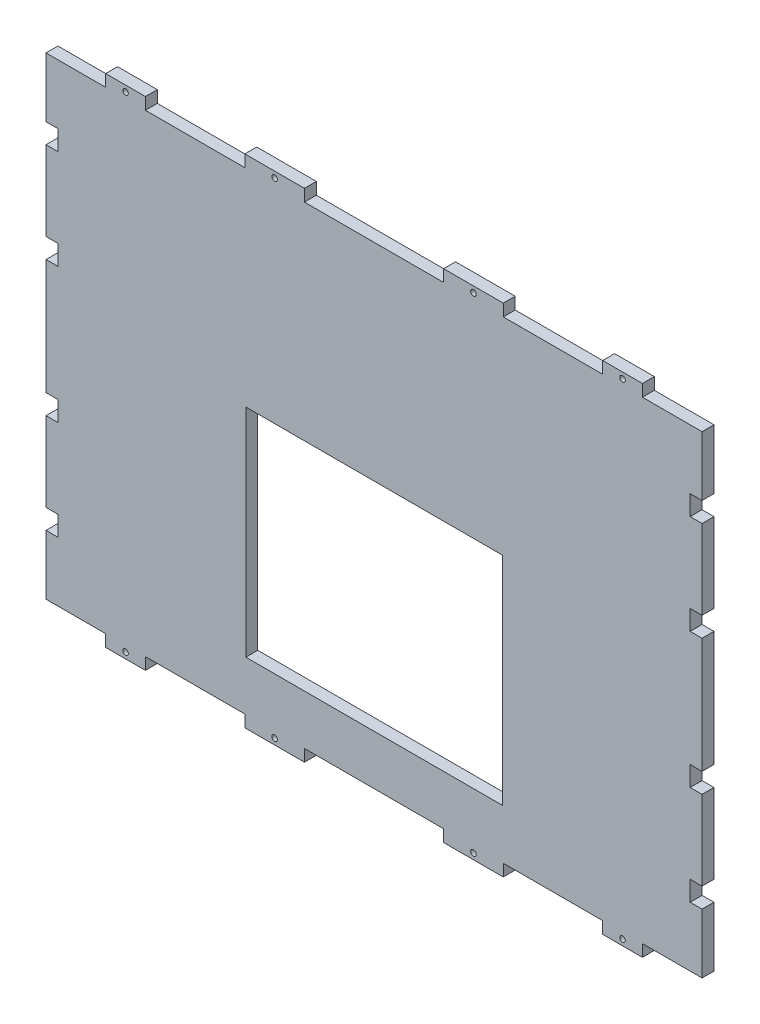
SolidWorks part; units mm, degrees
ref_plane "Plan de face" through (0, 0, 0) normal (0, 0, 1) x (1, 0, 0)
ref_plane "Plan de dessus" through (0, 0, 0) normal (0, 1, 0) x (1, 0, 0)
ref_plane "Plan de droite" through (0, 0, 0) normal (1, 0, 0) x (0, 0, -1)
sketch "Esquisse1" plane through (0, 0, 0) normal (0, 0, 1) x (1, 0, 0)
  line L0 (97.3951, 0) -> (-118.5049, 0) construction
  line L1 (-165, 119) -> (165, 119)
  line L2 (-165, 119) -> (-165, -119)
  line L3 (-165, -119) -> (165, -119)
  line L4 (165, 119) -> (165, -119)
  line L5 (0, 79.3588) -> (0, -79.3588) construction
  dimension "D1" = 238
  dimension "D2" = 330
  dimension "D3" = 165
  dimension "D4" = 119
extrude "Boss.-Extru.1" add sketch "Esquisse1" along normal blind 6
sketch "Esquisse2" plane through (0, 0, 6) normal (0, 0, 1) x (1, 0, 0)
  line L0 (-165, -119) -> (165, -119) construction
  line L1 (-64.5, 15) -> (64.5, 15)
  line L2 (-64.5, 15) -> (-64.5, -94)
  line L3 (-64.5, -94) -> (64.5, -94)
  line L4 (64.5, 15) -> (64.5, -94)
  line L5 (-165, 119) -> (-165, -119) construction
  dimension "D1" = 109
  dimension "D2" = 129
  dimension "D3" = 25
  dimension "D4" = 100.5
extrude "Enlèv. mat.-Extru.1" cut sketch "Esquisse2" against normal blind 6
sketch "Esquisse3" plane through (0, 0, 6) normal (0, 0, 1) x (1, 0, 0)
  line L0 (165, 119) -> (-165, 119) construction
  line L2 (-135, 119) -> (-135, 125)
  line L3 (-135, 125) -> (-115, 125)
  line L4 (-115, 119) -> (-115, 125)
  line L6 (-65, 119) -> (-35, 119)
  line L7 (-65, 119) -> (-65, 125)
  line L8 (-65, 125) -> (-35, 125)
  line L9 (-35, 119) -> (-35, 125)
  line L10 (-165, 119) -> (-165, -119) construction
  line L11 (0, 242.8959) -> (0, -237.5968) construction
  line L12 (383.215, 0) -> (-270.4786, 0) construction
  line L13 (35, 119) -> (35, 125)
  line L14 (65, 125) -> (35, 125)
  line L15 (65, 119) -> (65, 125)
  line L16 (65, 119) -> (35, 119)
  line L17 (115, 119) -> (115, 125)
  line L18 (135, 125) -> (115, 125)
  line L19 (135, 119) -> (135, 125)
  line L20 (135, 119) -> (115, 119)
  line L21 (-135, 119) -> (-115, 119)
  line L22 (-135, 119) -> (-135, 125)
  line L23 (-135, 125) -> (-115, 125)
  line L24 (-115, 119) -> (-115, 125)
  line L25 (-65, 119) -> (-35, 119)
  line L26 (-65, 119) -> (-65, 125)
  line L27 (-65, 125) -> (-35, 125)
  line L28 (-35, 119) -> (-35, 125)
  line L29 (35, 119) -> (35, 125)
  line L30 (65, 125) -> (35, 125)
  line L31 (65, 119) -> (65, 125)
  line L32 (65, 119) -> (35, 119)
  line L33 (115, 119) -> (115, 125)
  line L34 (135, 125) -> (115, 125)
  line L35 (135, 119) -> (135, 125)
  line L36 (135, 119) -> (115, 119)
  line L37 (135, -119) -> (115, -119)
  line L38 (135, -119) -> (135, -125)
  line L39 (135, -125) -> (115, -125)
  line L40 (115, -119) -> (115, -125)
  line L41 (65, -119) -> (35, -119)
  line L42 (65, -119) -> (65, -125)
  line L43 (65, -125) -> (35, -125)
  line L44 (35, -119) -> (35, -125)
  line L45 (-35, -119) -> (-35, -125)
  line L46 (-65, -125) -> (-35, -125)
  line L47 (-65, -119) -> (-65, -125)
  line L48 (-65, -119) -> (-35, -119)
  line L49 (-115, -119) -> (-115, -125)
  line L50 (-135, -125) -> (-115, -125)
  line L51 (-135, -119) -> (-135, -125)
  line L52 (-135, -119) -> (-115, -119)
  line L53 (135, -119) -> (115, -119)
  line L54 (135, -119) -> (135, -125)
  line L55 (135, -125) -> (115, -125)
  line L56 (115, -119) -> (115, -125)
  line L57 (65, -119) -> (35, -119)
  line L58 (65, -119) -> (65, -125)
  line L59 (65, -125) -> (35, -125)
  line L60 (35, -119) -> (35, -125)
  line L61 (-35, -119) -> (-35, -125)
  line L62 (-65, -125) -> (-35, -125)
  line L63 (-65, -119) -> (-65, -125)
  line L64 (-65, -119) -> (-35, -119)
  line L65 (-115, -119) -> (-115, -125)
  line L66 (-135, -125) -> (-115, -125)
  line L67 (-135, -119) -> (-135, -125)
  line L68 (-135, -119) -> (-115, -119)
  line M10 (-165, -119) -> (165, -119)
  line M12 (165, 119) -> (-165, 119)
  dimension "D1" = 20
  dimension "D2" = 6
  dimension "D3" = 6
  dimension "D4" = 30
  dimension "D5" = 50
  dimension "D6" = 30
extrude "Boss.-Extru.4" add sketch "Esquisse3" against normal blind 6 contours L4 L3 L2 M12 | L9 L8 L7 M12 | L15 L14 L13 M12 | L19 L18 L17 M12 | L40 L39 L38 M10 | L44 L43 L42 M10 | L47 L46 L45 M10 | L51 L50 L49 M10
sketch "Esquisse4" plane through (0, 0, 6) normal (0, 0, 1) x (1, 0, 0)
  line L0 (-165, 119) -> (-165, -119) construction
  line L1 (-165, 89) -> (-159, 89)
  line L2 (-165, 89) -> (-165, 79)
  line L3 (-165, 79) -> (-159, 79)
  line L4 (-159, 89) -> (-159, 79)
  line L5 (-135, 119) -> (-165, 119) construction
  line L6 (-165, 39) -> (-159, 39)
  line L7 (-165, 39) -> (-165, 29)
  line L8 (-165, 29) -> (-159, 29)
  line L9 (-159, 39) -> (-159, 29)
  line L12 (258.3547, 0) -> (-305.8943, 0) construction
  line L13 (0, -179.773) -> (0, 204.7522) construction
  line L14 (-159, -89) -> (-159, -79)
  line L15 (-165, -89) -> (-159, -89)
  line L16 (-159, -39) -> (-159, -29)
  line L17 (-165, -29) -> (-159, -29)
  line L18 (-165, -39) -> (-165, -29)
  line L19 (-165, -39) -> (-159, -39)
  line L20 (-165, -79) -> (-159, -79)
  line L21 (-165, -89) -> (-165, -79)
  line L22 (165, -89) -> (165, -79)
  line L23 (165, -79) -> (159, -79)
  line L24 (165, -39) -> (159, -39)
  line L25 (165, -39) -> (165, -29)
  line L26 (165, -29) -> (159, -29)
  line L27 (159, -39) -> (159, -29)
  line L28 (165, -89) -> (159, -89)
  line L29 (159, -89) -> (159, -79)
  line L30 (159, 39) -> (159, 29)
  line L31 (165, 29) -> (159, 29)
  line L32 (165, 39) -> (165, 29)
  line L33 (165, 39) -> (159, 39)
  line L34 (159, 89) -> (159, 79)
  line L35 (165, 79) -> (159, 79)
  line L36 (165, 89) -> (165, 79)
  line L37 (165, 89) -> (159, 89)
  dimension "D1" = 30
  dimension "D2" = 10
  dimension "D3" = 10
  dimension "D4" = 40
  dimension "D5" = 6
  dimension "D6" = 6
extrude "Enlèv. mat.-Extru.3" cut sketch "Esquisse4" against normal blind 6
sketch "Esquisse5" plane through (0, 0, 6) normal (0, 0, 1) x (1, 0, 0)
  line L0 (0, 191.4631) -> (0, -169.6008) construction
  line L1 (329.1421, 0) -> (-255.0592, 0) construction
  line L2 (-115, 119) -> (-115, 125) construction
  line L4 (-35, 119) -> (-35, 125) construction
  line L5 (-65, 125) -> (-35, 125) construction
  circle A0 centre (-125, 122) radius 1.4
  circle A1 centre (-50, 122) radius 1.4
  circle A2 centre (50, 122) radius 1.4
  circle A3 centre (125, 122) radius 1.4
  circle A4 centre (125, -122) radius 1.4
  circle A5 centre (50, -122) radius 1.4
  circle A6 centre (-50, -122) radius 1.4
  circle A7 centre (-125, -122) radius 1.4
  dimension "D1" = 2.8
  dimension "D2" = 10
  dimension "D4" = 2.8
  dimension "D5" = 15
  dimension "D6" = 3
extrude "Enlèv. mat.-Extru.4" cut sketch "Esquisse5" against normal blind 6
equation "\"D3@Esquisse1\"=\"D2@Esquisse1\"/2"
equation "\"D4@Esquisse1\"=\"D1@Esquisse1\"/2"
equation "\"D4@Esquisse2\"=(\"D2@Esquisse1\"-\"D2@Esquisse2\")/2"
